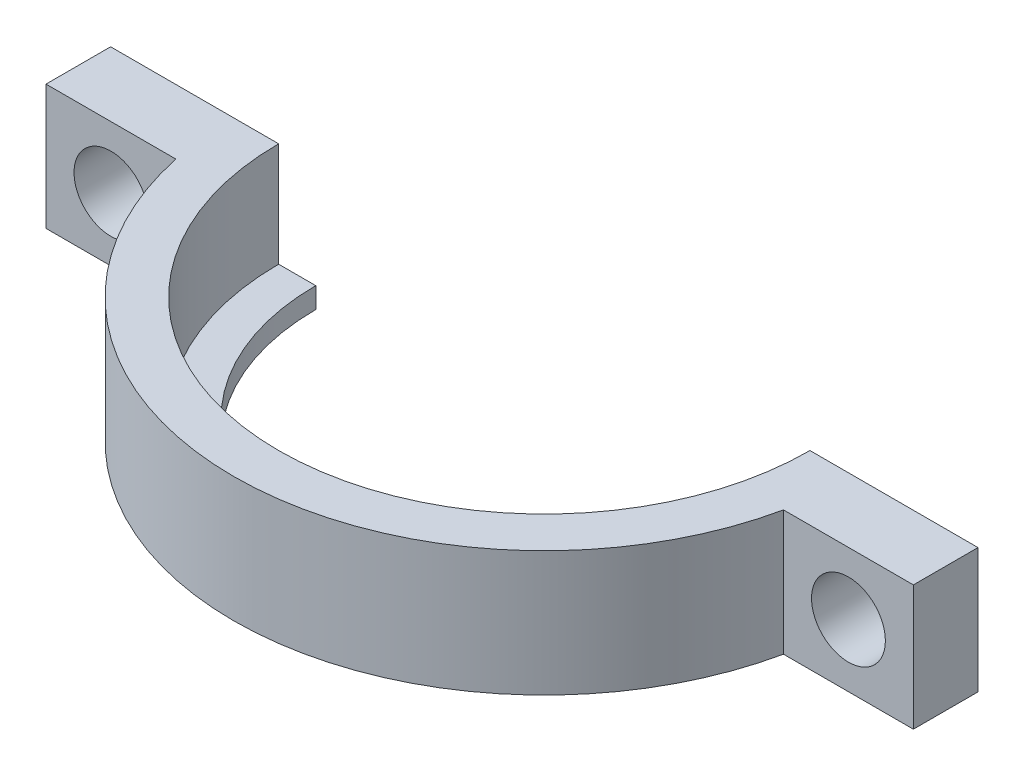
SolidWorks part; units mm, degrees
ref_plane "Front Plane" through (0, 0, 0) normal (0, 0, 1) x (1, 0, 0)
ref_plane "Top Plane" through (0, 0, 0) normal (0, 1, 0) x (1, 0, 0)
ref_plane "Right Plane" through (0, 0, 0) normal (1, 0, 0) x (0, 0, -1)
sketch "Sketch3" plane through (0, 0, 0) normal (0, 0, 1) x (1, 0, 0)
  line L0 (-62.6943, 10.2507) -> (-62.6943, 11.7337)
  line L2 (-62.6943, 11.7337) -> (-64.8845, 11.7337)
  line L5 (-60.8845, 6.6507) -> (-62.6943, 6.6507)
  line L6 (-62.6943, 6.6507) -> (-62.6943, 10.2507)
  line L10 (-64.8845, 11.7337) -> (-64.8845, 5.6398)
  line L11 (-64.8845, 5.6398) -> (-60.8845, 5.6398)
  line L12 (-60.8845, 5.6398) -> (-60.8845, 6.6507)
  dimension "D3" = 4
sketch "Sketch4" plane through (0, 0, 0) normal (0, 0, 1) x (1, 0, 0)
  line L0 (-49.7443, 0) -> (-49.7443, 12.8648) construction
  line L1 (27.6543, 0) -> (-27.6543, 0) construction
revolve "Revolve1" add sketch "Sketch3" angle 360 about L0
sketch "Sketch7" plane through (0, 11.7337, 0) normal (0, 1, 0) x (1, 0, 0)
  line L2 (-50.2443, 15.132) -> (-50.2443, 12.9403)
  line L3 (-49.2443, 15.132) -> (-49.2443, 12.9403)
  circle A0 centre (-49.7443, 0) radius 15.1403 construction
  arc A1 (-49.2443, 15.132) -> (-50.2443, 15.132) centre (-49.7443, 0) ccw
  circle A2 centre (-49.7443, 0) radius 12.95 construction
  arc A3 (-49.2443, 12.9403) -> (-50.2443, 12.9403) centre (-49.7443, 0) ccw
  point P9 (-49.7443, 14.131)
  dimension "D1" = 1
extrude "Boss-Extrude1" add sketch "Sketch7" along normal blind 5
sketch "Sketch8" plane through (0, 16.7337, 0) normal (0, 1, 0) x (1, 0, 0)
  line L0 (-50.2443, 15.132) -> (-50.2443, 12.9403) construction
  line L3 (-50.2443, 15.132) -> (-50.2443, 12.9403)
  line L4 (-49.2443, 12.9403) -> (-49.2443, 15.132) construction
  line L5 (-49.2443, 12.9403) -> (-49.2443, 15.132)
  line L6 (-50.2443, 12.9403) -> (-50.2443, -4.5597)
  line L7 (-50.2443, -4.5597) -> (-49.2443, -4.5597)
  line L8 (-49.2443, -4.5597) -> (-49.2443, 12.9403)
  arc A0 (-49.2443, 15.132) -> (-50.2443, 15.132) centre (-49.7443, 0) ccw construction
  arc A1 (-49.2443, 15.132) -> (-50.2443, 15.132) centre (-49.7443, 0) ccw
  dimension "D1" = 17.5
extrude "Boss-Extrude2" add sketch "Sketch8" against normal blind 3
sketch "Sketch9" plane through (0, 11.7337, 0) normal (0, 1, 0) x (1, 0, 0)
  line L2 (-54.4943, 14.3759) -> (-54.4943, 39.3759)
  line L3 (-54.4943, 39.3759) -> (-44.9943, 39.3759)
  line L4 (-44.9943, 39.3759) -> (-44.9943, 14.3759)
  arc A0 (-50.2443, 15.132) -> (-49.2443, 15.132) centre (-49.7443, 0) ccw construction
  arc A1 (-50.2443, 15.132) -> (-54.4943, 14.3759) centre (-49.7443, 0) ccw
  arc A2 (-49.2443, 15.132) -> (-50.2443, 15.132) centre (-49.7443, 0) ccw construction
  arc A3 (-49.2443, 15.132) -> (-50.2443, 15.132) centre (-49.7443, 0) ccw
  arc A4 (-44.9943, 14.3759) -> (-49.2443, 15.132) centre (-49.7443, 0) ccw
  point P9 (-49.7443, 0)
  dimension "D1" = 25
extrude "Boss-Extrude3" add sketch "Sketch9" against normal blind 3
sketch "Sketch10" plane through (0, 8.7337, 0) normal (0, -1, 0) x (1, 0, 0)
  line L0 (-44.9943, -14.3759) -> (-44.9943, -39.3759) construction
  line L1 (-54.4943, -39.3759) -> (-44.9943, -39.3759)
  line L2 (-54.4943, -39.3759) -> (-54.4943, -34.3759)
  line L3 (-54.4943, -34.3759) -> (-44.9943, -34.3759)
  line L4 (-44.9943, -39.3759) -> (-44.9943, -34.3759)
  dimension "D1" = 5
extrude "Boss-Extrude4" add sketch "Sketch10" along normal blind 15.78
sketch "Sketch11" plane through (0, 0, -39.3759) normal (0, 0, -1) x (-1, 0, 0)
  line L0 (54.4943, -7.0463) -> (54.4943, 11.7337) construction
  line L1 (44.9943, -7.0463) -> (54.4943, -7.0463)
  line L2 (44.9943, -7.0463) -> (44.9943, -5.0463)
  line L3 (44.9943, -5.0463) -> (54.4943, -5.0463)
  line L4 (54.4943, -7.0463) -> (54.4943, -5.0463)
  dimension "D1" = 2
extrude "Boss-Extrude5" add sketch "Sketch11" along normal blind 40
sketch "Sketch13" plane through (0, 11.7337, 0) normal (0, 1, 0) x (1, 0, 0)
  line L2 (-49.7443, 3.15) -> (-49.7443, -3.15) construction
  line L3 (-28.604, 3.15) -> (-34.9353, 3.15)
  line L4 (-70.8845, 3.15) -> (-70.8845, -3.15)
  line L5 (-70.8845, -3.15) -> (-64.5532, -3.15)
  line L6 (-28.604, -3.15) -> (-28.604, 3.15)
  line L7 (-64.5532, 3.15) -> (-70.8845, 3.15)
  line L8 (-34.9353, -3.15) -> (-28.604, -3.15)
  arc A0 (-54.4943, 14.3759) -> (-44.9943, 14.3759) centre (-49.7443, 0) ccw construction
  arc A1 (-64.5532, 3.15) -> (-64.5532, -3.15) centre (-49.7443, 0) ccw
  arc A2 (-34.9353, -3.15) -> (-34.9353, 3.15) centre (-49.7443, 0) ccw
  point P10 (-49.7443, 0)
  point P13 (-49.7443, 3.15)
  dimension "D1" = 6.3
extrude "Boss-Extrude6" add sketch "Sketch13" against normal up to surface (6.0939 mm away) up to face at (-49.7443, 5.6398, -11.1403)
sketch "Sketch14" plane through (0, 0, 3.15) normal (0, 0, 1) x (1, 0, 0)
  line L0 (-70.8845, 11.7337) -> (-64.5532, 5.6398) construction
  line L1 (-28.604, 11.7337) -> (-34.9353, 5.6398) construction
  circle A0 centre (-31.7697, 8.6868) radius 1.8
  circle A1 centre (-67.7189, 8.6868) radius 1.8
  dimension "D1" = 3.6
  dimension "D2" = 3.6
extrude "Cut-Extrude1" cut sketch "Sketch14" against normal up to surface (6.3 mm away) contours A1 | A0 up to face at (-67.7189, 8.6868, -3.15)
sketch "Sketch15" plane through (0, 11.7337, 0) normal (0, 1, 0) x (1, 0, 0)
  line L0 (-70.8845, 0) -> (-23.4421, 0) construction
  line L1 (-70.8845, 3.15) -> (-70.8845, -3.15) construction
  line L2 (-13.079, 0) -> (13.079, 0) construction
  line L4 (-23.4421, 0) -> (-74.5953, 0)
  line L5 (-23.4421, 0) -> (-23.4421, 86.0506)
  line L6 (-23.4421, 86.0506) -> (-74.5953, 86.0506)
  line L7 (-74.5953, 0) -> (-74.5953, 86.0506)
extrude "Cut-Extrude3" cut sketch "Sketch15" against normal through all both and the other way through all
sketch "Sketch16" plane through (0, 0, 0) normal (0, 1, 0) x (1, 0, 0)
  line L1 (-54.8883, 5.4174) -> (-45.2843, 5.4174)
  line L2 (-54.8883, 5.4174) -> (-54.8883, -6.4675)
  line L3 (-54.8883, -6.4675) -> (-45.2843, -6.4675)
  line L4 (-45.2843, 5.4174) -> (-45.2843, -6.4675)
extrude "Cut-Extrude4" cut sketch "Sketch16" along normal through all
